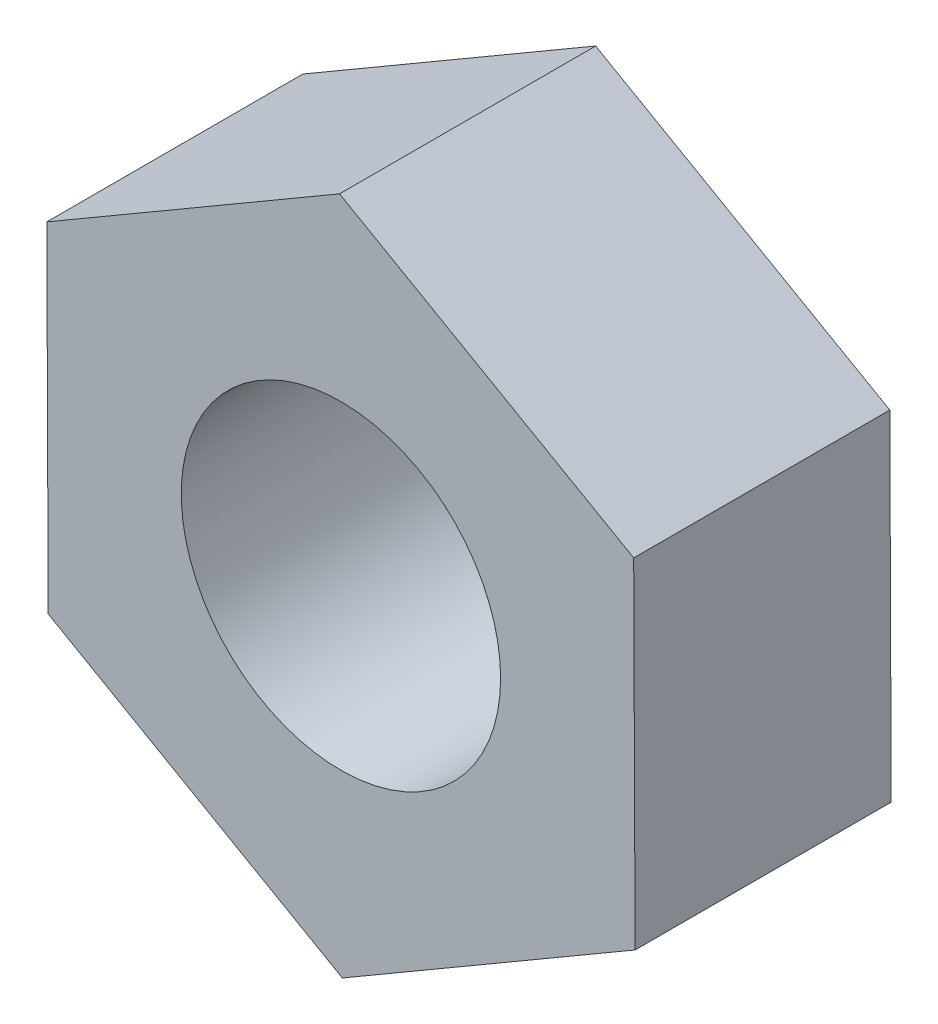
SolidWorks part; units mm, degrees
material "Stop odlewniczy stali"
ref_plane "Płaszczyzna przednia" through (0, 0, 0) normal (0, 0, 1) x (1, 0, 0)
ref_plane "Płaszczyzna górna" through (0, 0, 0) normal (0, 1, 0) x (1, 0, 0)
ref_plane "Płaszczyzna prawa" through (0, 0, 0) normal (1, 0, 0) x (0, 0, -1)
sketch "Szkic1" plane through (0, 0, 0) normal (0, 0, 1) x (1, 0, 0)
  line L1 (2.7434, 1.599) -> (-0.0131, 3.1754)
  line L2 (-0.0131, 3.1754) -> (-2.7565, 1.5764)
  line L3 (-2.7565, 1.5764) -> (-2.7434, -1.599)
  line L4 (-2.7434, -1.599) -> (0.0131, -3.1754)
  line L5 (0.0131, -3.1754) -> (2.7565, -1.5764)
  line L6 (2.7565, -1.5764) -> (2.7434, 1.599)
  circle A0 centre (0, 0) radius 1.4964
  circle A1 centre (0, 0) radius 2.75 construction
  circle A2 centre (0, 0) radius 2.75 construction
  dimension "D1" = 5.5
  dimension "D2" = 5.5
extrude "Dodanie-wyciągnięcie1" add sketch "Szkic1" along normal blind 2.4
